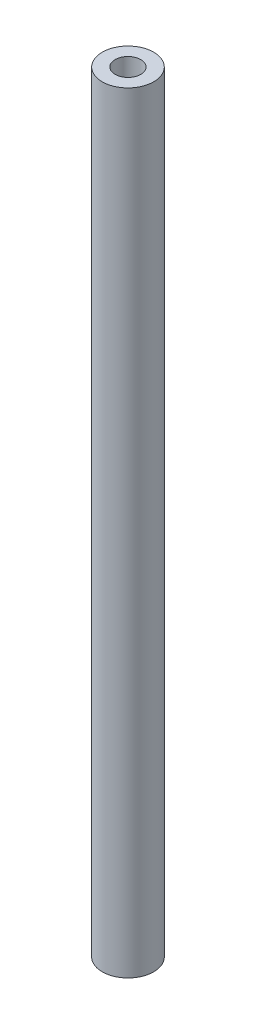
SolidWorks part; units mm, degrees
material "PE High Density"
ref_plane "Front Plane" through (0, 0, 0) normal (0, 0, 1) x (1, 0, 0)
ref_plane "Top Plane" through (0, 0, 0) normal (0, 1, 0) x (1, 0, 0)
ref_plane "Right Plane" through (0, 0, 0) normal (1, 0, 0) x (0, 0, -1)
sketch "Sketch1" plane through (0, 0, 0) normal (0, 1, 0) x (1, 0, 0)
  circle A0 centre (0, 0) radius 12.7
  circle A1 centre (0, 0) radius 6.35
  dimension "D1" = 25.4
  dimension "D2" = 12.7
extrude "Boss-Extrude1" add sketch "Sketch1" along normal blind 381 contours A0 | A1
